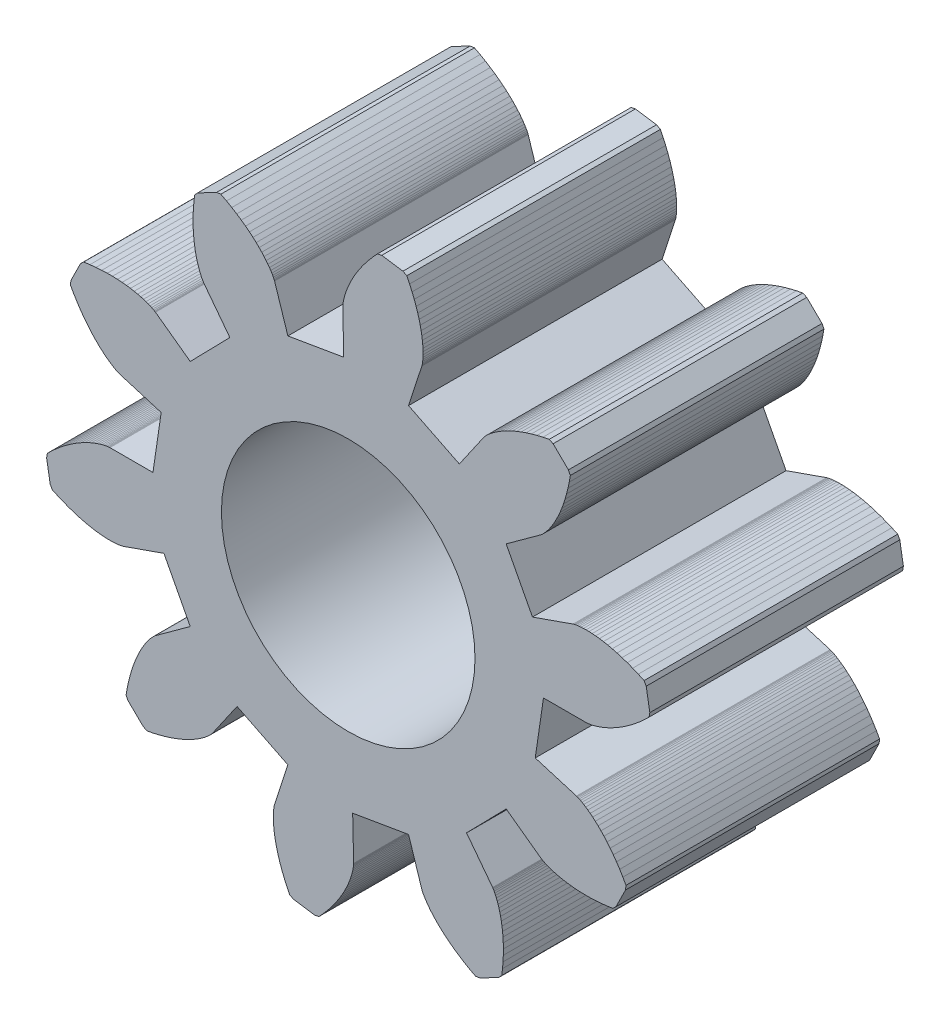
SolidWorks part; units mm, degrees
ref_plane "前基準面" through (0, 0, 0) normal (0, 0, 1) x (1, 0, 0)
ref_plane "上基準面" through (0, 0, 0) normal (0, 1, 0) x (1, 0, 0)
ref_plane "右基準面" through (0, 0, 0) normal (1, 0, 0) x (0, 0, -1)
sketch "Model" plane through (0, 0, 0) normal (0, 0, 1) x (1, 0, 0)
  line L0 (3.85, 0) -> (4.6992, 0)
  line L1 (4.6992, 0) -> (4.7049, 0.0002)
  line L2 (4.7049, 0.0002) -> (4.7163, 0.001)
  line L3 (4.7163, 0.001) -> (4.7334, 0.0029)
  line L4 (4.7334, 0.0029) -> (4.7561, 0.0061)
  line L5 (4.7561, 0.0061) -> (4.7843, 0.011)
  line L6 (4.7843, 0.011) -> (4.8179, 0.0182)
  line L7 (4.8179, 0.0182) -> (4.8567, 0.0279)
  line L8 (4.8567, 0.0279) -> (4.9007, 0.0405)
  line L9 (4.9007, 0.0405) -> (4.9497, 0.0565)
  line L10 (4.9497, 0.0565) -> (5.0035, 0.0761)
  line L11 (5.0035, 0.0761) -> (5.0619, 0.0997)
  line L12 (5.0619, 0.0997) -> (5.1247, 0.1276)
  line L13 (5.1247, 0.1276) -> (5.1915, 0.1603)
  line L14 (5.1915, 0.1603) -> (5.2623, 0.1979)
  line L15 (5.2623, 0.1979) -> (5.3367, 0.2409)
  line L16 (5.3367, 0.2409) -> (5.4143, 0.2894)
  line L17 (5.4143, 0.2894) -> (5.495, 0.3439)
  line L18 (5.495, 0.3439) -> (5.5783, 0.4044)
  line L19 (5.5783, 0.4044) -> (5.664, 0.4714)
  line L20 (5.664, 0.4714) -> (5.7517, 0.545)
  line L21 (5.7517, 0.545) -> (5.8411, 0.6255)
  line L22 (5.8411, 0.6255) -> (5.9317, 0.713)
  line L23 (5.9317, 0.713) -> (5.9468, 0.7975)
  line L24 (5.9468, 0.7975) -> (5.876, 1.2136)
  line L25 (5.876, 1.2136) -> (5.8338, 1.2884)
  line L26 (5.8338, 1.2884) -> (5.7194, 1.341)
  line L27 (5.7194, 1.341) -> (5.6085, 1.3874)
  line L28 (5.6085, 1.3874) -> (5.5014, 1.4279)
  line L29 (5.5014, 1.4279) -> (5.3983, 1.4627)
  line L30 (5.3983, 1.4627) -> (5.2996, 1.4924)
  line L31 (5.2996, 1.4924) -> (5.2055, 1.517)
  line L32 (5.2055, 1.517) -> (5.1161, 1.5372)
  line L33 (5.1161, 1.5372) -> (5.0318, 1.5531)
  line L34 (5.0318, 1.5531) -> (4.9525, 1.5653)
  line L35 (4.9525, 1.5653) -> (4.8786, 1.574)
  line L36 (4.8786, 1.574) -> (4.8102, 1.5796)
  line L37 (4.8102, 1.5796) -> (4.7473, 1.5826)
  line L38 (4.7473, 1.5826) -> (4.69, 1.5833)
  line L39 (4.69, 1.5833) -> (4.6385, 1.5821)
  line L40 (4.6385, 1.5821) -> (4.5928, 1.5795)
  line L41 (4.5928, 1.5795) -> (4.5529, 1.5758)
  line L42 (4.5529, 1.5758) -> (4.5188, 1.5714)
  line L43 (4.5188, 1.5714) -> (4.4906, 1.5668)
  line L44 (4.4906, 1.5668) -> (4.4681, 1.5624)
  line L45 (4.4681, 1.5624) -> (4.4514, 1.5584)
  line L46 (4.4514, 1.5584) -> (4.4404, 1.5554)
  line L47 (4.4404, 1.5554) -> (4.4349, 1.5537)
  line L48 (4.4349, 1.5537) -> (3.6335, 1.273)
  line L49 (3.6335, 1.273) -> (3.1147, 2.263)
  line L50 (3.1147, 2.263) -> (3.8017, 2.7621)
  line L51 (3.8017, 2.7621) -> (3.8062, 2.7657)
  line L52 (3.8062, 2.7657) -> (3.815, 2.773)
  line L53 (3.815, 2.773) -> (3.8277, 2.7845)
  line L54 (3.8277, 2.7845) -> (3.8442, 2.8004)
  line L55 (3.8442, 2.8004) -> (3.8641, 2.821)
  line L56 (3.8641, 2.821) -> (3.887, 2.8466)
  line L57 (3.887, 2.8466) -> (3.9128, 2.8773)
  line L58 (3.9128, 2.8773) -> (3.941, 2.9134)
  line L59 (3.941, 2.9134) -> (3.9712, 2.9551)
  line L60 (3.9712, 2.9551) -> (4.0032, 3.0026)
  line L61 (4.0032, 3.0026) -> (4.0366, 3.056)
  line L62 (4.0366, 3.056) -> (4.0709, 3.1155)
  line L63 (4.0709, 3.1155) -> (4.1058, 3.1812)
  line L64 (4.1058, 3.1812) -> (4.141, 3.2532)
  line L65 (4.141, 3.2532) -> (4.1759, 3.3317)
  line L66 (4.1759, 3.3317) -> (4.2102, 3.4166)
  line L67 (4.2102, 3.4166) -> (4.2434, 3.5081)
  line L68 (4.2434, 3.5081) -> (4.2753, 3.6061)
  line L69 (4.2753, 3.6061) -> (4.3052, 3.7106)
  line L70 (4.3052, 3.7106) -> (4.3329, 3.8217)
  line L71 (4.3329, 3.8217) -> (4.3579, 3.9393)
  line L72 (4.3579, 3.9393) -> (4.3797, 4.0633)
  line L73 (4.3797, 4.0633) -> (4.3423, 4.1406)
  line L74 (4.3423, 4.1406) -> (4.0404, 4.4357)
  line L75 (4.0404, 4.4357) -> (3.9623, 4.4713)
  line L76 (3.9623, 4.4713) -> (3.8388, 4.4466)
  line L77 (3.8388, 4.4466) -> (3.7218, 4.419)
  line L78 (3.7218, 4.419) -> (3.6114, 4.3888)
  line L79 (3.6114, 4.3888) -> (3.5076, 4.3564)
  line L80 (3.5076, 4.3564) -> (3.4103, 4.3224)
  line L81 (3.4103, 4.3224) -> (3.3196, 4.287)
  line L82 (3.3196, 4.287) -> (3.2355, 4.2508)
  line L83 (3.2355, 4.2508) -> (3.1579, 4.2141)
  line L84 (3.1579, 4.2141) -> (3.0867, 4.1774)
  line L85 (3.0867, 4.1774) -> (3.0218, 4.1409)
  line L86 (3.0218, 4.1409) -> (2.963, 4.1053)
  line L87 (2.963, 4.1053) -> (2.9104, 4.0707)
  line L88 (2.9104, 4.0707) -> (2.8637, 4.0376)
  line L89 (2.8637, 4.0376) -> (2.8227, 4.0064)
  line L90 (2.8227, 4.0064) -> (2.7873, 3.9774)
  line L91 (2.7873, 3.9774) -> (2.7571, 3.951)
  line L92 (2.7571, 3.951) -> (2.7321, 3.9274)
  line L93 (2.7321, 3.9274) -> (2.712, 3.9071)
  line L94 (2.712, 3.9071) -> (2.6965, 3.8903)
  line L95 (2.6965, 3.8903) -> (2.6852, 3.8773)
  line L96 (2.6852, 3.8773) -> (2.6781, 3.8683)
  line L97 (2.6781, 3.8683) -> (2.6746, 3.8638)
  line L98 (2.6746, 3.8638) -> (2.1913, 3.1655)
  line L99 (2.1913, 3.1655) -> (1.1897, 3.6616)
  line L100 (1.1897, 3.6616) -> (1.4521, 4.4692)
  line L101 (1.4521, 4.4692) -> (1.4537, 4.4747)
  line L102 (1.4537, 4.4747) -> (1.4564, 4.4858)
  line L103 (1.4564, 4.4858) -> (1.46, 4.5026)
  line L104 (1.46, 4.5026) -> (1.4639, 4.5252)
  line L105 (1.4639, 4.5252) -> (1.4679, 4.5535)
  line L106 (1.4679, 4.5535) -> (1.4715, 4.5877)
  line L107 (1.4715, 4.5877) -> (1.4743, 4.6276)
  line L108 (1.4743, 4.6276) -> (1.4758, 4.6734)
  line L109 (1.4758, 4.6734) -> (1.4758, 4.7249)
  line L110 (1.4758, 4.7249) -> (1.4738, 4.7822)
  line L111 (1.4738, 4.7822) -> (1.4694, 4.845)
  line L112 (1.4694, 4.845) -> (1.4622, 4.9133)
  line L113 (1.4622, 4.9133) -> (1.4518, 4.987)
  line L114 (1.4518, 4.987) -> (1.4379, 5.0659)
  line L115 (1.4379, 5.0659) -> (1.42, 5.1499)
  line L116 (1.42, 5.1499) -> (1.3979, 5.2388)
  line L117 (1.3979, 5.2388) -> (1.371, 5.3323)
  line L118 (1.371, 5.3323) -> (1.3392, 5.4303)
  line L119 (1.3392, 5.4303) -> (1.3019, 5.5325)
  line L120 (1.3019, 5.5325) -> (1.259, 5.6387)
  line L121 (1.259, 5.6387) -> (1.2101, 5.7485)
  line L122 (1.2101, 5.7485) -> (1.1549, 5.8617)
  line L123 (1.1549, 5.8617) -> (1.0792, 5.9021)
  line L124 (1.0792, 5.9021) -> (0.6615, 5.9634)
  line L125 (0.6615, 5.9634) -> (0.5774, 5.9464)
  line L126 (0.5774, 5.9464) -> (0.492, 5.8538)
  line L127 (0.492, 5.8538) -> (0.4136, 5.7627)
  line L128 (0.4136, 5.7627) -> (0.342, 5.6733)
  line L129 (0.342, 5.6733) -> (0.277, 5.5861)
  line L130 (0.277, 5.5861) -> (0.2184, 5.5014)
  line L131 (0.2184, 5.5014) -> (0.1658, 5.4195)
  line L132 (0.1658, 5.4195) -> (0.119, 5.3408)
  line L133 (0.119, 5.3408) -> (0.0778, 5.2654)
  line L134 (0.0778, 5.2654) -> (0.0418, 5.1938)
  line L135 (0.0418, 5.1938) -> (0.0107, 5.1262)
  line L136 (0.0107, 5.1262) -> (-0.0159, 5.0629)
  line L137 (-0.0159, 5.0629) -> (-0.0381, 5.004)
  line L138 (-0.0381, 5.004) -> (-0.0565, 4.9497)
  line L139 (-0.0565, 4.9497) -> (-0.0713, 4.9004)
  line L140 (-0.0713, 4.9004) -> (-0.0829, 4.8561)
  line L141 (-0.0829, 4.8561) -> (-0.0918, 4.817)
  line L142 (-0.0918, 4.817) -> (-0.0981, 4.7833)
  line L143 (-0.0981, 4.7833) -> (-0.1025, 4.755)
  line L144 (-0.1025, 4.755) -> (-0.1052, 4.7322)
  line L145 (-0.1052, 4.7322) -> (-0.1066, 4.7151)
  line L146 (-0.1066, 4.7151) -> (-0.1071, 4.7037)
  line L147 (-0.1071, 4.7037) -> (-0.1072, 4.698)
  line L148 (-0.1072, 4.698) -> (-0.0879, 3.849)
  line L149 (-0.0879, 3.849) -> (-1.1897, 3.6616)
  line L150 (-1.1897, 3.6616) -> (-1.4521, 4.4692)
  line L151 (-1.4521, 4.4692) -> (-1.4541, 4.4746)
  line L152 (-1.4541, 4.4746) -> (-1.4584, 4.4852)
  line L153 (-1.4584, 4.4852) -> (-1.4654, 4.5008)
  line L154 (-1.4654, 4.5008) -> (-1.4755, 4.5214)
  line L155 (-1.4755, 4.5214) -> (-1.4889, 4.5467)
  line L156 (-1.4889, 4.5467) -> (-1.5061, 4.5764)
  line L157 (-1.5061, 4.5764) -> (-1.5274, 4.6104)
  line L158 (-1.5274, 4.6104) -> (-1.553, 4.6484)
  line L159 (-1.553, 4.6484) -> (-1.5833, 4.69)
  line L160 (-1.5833, 4.69) -> (-1.6185, 4.7351)
  line L161 (-1.6185, 4.7351) -> (-1.659, 4.7834)
  line L162 (-1.659, 4.7834) -> (-1.705, 4.8344)
  line L163 (-1.705, 4.8344) -> (-1.7567, 4.8879)
  line L164 (-1.7567, 4.8879) -> (-1.8144, 4.9436)
  line L165 (-1.8144, 4.9436) -> (-1.8782, 5.001)
  line L166 (-1.8782, 5.001) -> (-1.9484, 5.0599)
  line L167 (-1.9484, 5.0599) -> (-2.0251, 5.1198)
  line L168 (-2.0251, 5.1198) -> (-2.1084, 5.1803)
  line L169 (-2.1084, 5.1803) -> (-2.1986, 5.2412)
  line L170 (-2.1986, 5.2412) -> (-2.2957, 5.3018)
  line L171 (-2.2957, 5.3018) -> (-2.3999, 5.3619)
  line L172 (-2.3999, 5.3619) -> (-2.5111, 5.421)
  line L173 (-2.5111, 5.421) -> (-2.5961, 5.4093)
  line L174 (-2.5961, 5.4093) -> (-2.97, 5.2134)
  line L175 (-2.97, 5.2134) -> (-3.0281, 5.1501)
  line L176 (-3.0281, 5.1501) -> (-3.0427, 5.025)
  line L177 (-3.0427, 5.025) -> (-3.0526, 4.9052)
  line L178 (-3.0526, 4.9052) -> (-3.058, 4.7909)
  line L179 (-3.058, 4.7909) -> (-3.0593, 4.6821)
  line L180 (-3.0593, 4.6821) -> (-3.057, 4.5791)
  line L181 (-3.057, 4.5791) -> (-3.0514, 4.4819)
  line L182 (-3.0514, 4.4819) -> (-3.0429, 4.3907)
  line L183 (-3.0429, 4.3907) -> (-3.032, 4.3056)
  line L184 (-3.032, 4.3056) -> (-3.0191, 4.2265)
  line L185 (-3.0191, 4.2265) -> (-3.0045, 4.1535)
  line L186 (-3.0045, 4.1535) -> (-2.9887, 4.0866)
  line L187 (-2.9887, 4.0866) -> (-2.9721, 4.0259)
  line L188 (-2.9721, 4.0259) -> (-2.9551, 3.9712)
  line L189 (-2.9551, 3.9712) -> (-2.9381, 3.9226)
  line L190 (-2.9381, 3.9226) -> (-2.9214, 3.8799)
  line L191 (-2.9214, 3.8799) -> (-2.9056, 3.8431)
  line L192 (-2.9056, 3.8431) -> (-2.8909, 3.8121)
  line L193 (-2.8909, 3.8121) -> (-2.8778, 3.7866)
  line L194 (-2.8778, 3.7866) -> (-2.8666, 3.7666)
  line L195 (-2.8666, 3.7666) -> (-2.8577, 3.752)
  line L196 (-2.8577, 3.752) -> (-2.8514, 3.7424)
  line L197 (-2.8514, 3.7424) -> (-2.8481, 3.7377)
  line L198 (-2.8481, 3.7377) -> (-2.3335, 3.0623)
  line L199 (-2.3335, 3.0623) -> (-3.1147, 2.263)
  line L200 (-3.1147, 2.263) -> (-3.8017, 2.7621)
  line L201 (-3.8017, 2.7621) -> (-3.8065, 2.7653)
  line L202 (-3.8065, 2.7653) -> (-3.8162, 2.7713)
  line L203 (-3.8162, 2.7713) -> (-3.8311, 2.7799)
  line L204 (-3.8311, 2.7799) -> (-3.8513, 2.7906)
  line L205 (-3.8513, 2.7906) -> (-3.877, 2.8032)
  line L206 (-3.877, 2.8032) -> (-3.9084, 2.8171)
  line L207 (-3.9084, 2.8171) -> (-3.9456, 2.8321)
  line L208 (-3.9456, 2.8321) -> (-3.9886, 2.8478)
  line L209 (-3.9886, 2.8478) -> (-4.0376, 2.8637)
  line L210 (-4.0376, 2.8637) -> (-4.0927, 2.8795)
  line L211 (-4.0927, 2.8795) -> (-4.1538, 2.8947)
  line L212 (-4.1538, 2.8947) -> (-4.221, 2.9089)
  line L213 (-4.221, 2.9089) -> (-4.2943, 2.9218)
  line L214 (-4.2943, 2.9218) -> (-4.3736, 2.933)
  line L215 (-4.3736, 2.933) -> (-4.459, 2.9419)
  line L216 (-4.459, 2.9419) -> (-4.5504, 2.9483)
  line L217 (-4.5504, 2.9483) -> (-4.6477, 2.9517)
  line L218 (-4.6477, 2.9517) -> (-4.7507, 2.9517)
  line L219 (-4.7507, 2.9517) -> (-4.8594, 2.9479)
  line L220 (-4.8594, 2.9479) -> (-4.9736, 2.9399)
  line L221 (-4.9736, 2.9399) -> (-5.0932, 2.9273)
  line L222 (-5.0932, 2.9273) -> (-5.2179, 2.9097)
  line L223 (-5.2179, 2.9097) -> (-5.2798, 2.8503)
  line L224 (-5.2798, 2.8503) -> (-5.4671, 2.472)
  line L225 (-5.4671, 2.472) -> (-5.4769, 2.3867)
  line L226 (-5.4769, 2.3867) -> (-5.4153, 2.2769)
  line L227 (-5.4153, 2.2769) -> (-5.3528, 2.1741)
  line L228 (-5.3528, 2.1741) -> (-5.29, 2.0784)
  line L229 (-5.29, 2.0784) -> (-5.2271, 1.9897)
  line L230 (-5.2271, 1.9897) -> (-5.1647, 1.9077)
  line L231 (-5.1647, 1.9077) -> (-5.103, 1.8324)
  line L232 (-5.103, 1.8324) -> (-5.0426, 1.7636)
  line L233 (-5.0426, 1.7636) -> (-4.9837, 1.7011)
  line L234 (-4.9837, 1.7011) -> (-4.9267, 1.6447)
  line L235 (-4.9267, 1.6447) -> (-4.872, 1.5942)
  line L236 (-4.872, 1.5942) -> (-4.82, 1.5494)
  line L237 (-4.82, 1.5494) -> (-4.7708, 1.5101)
  line L238 (-4.7708, 1.5101) -> (-4.7249, 1.4758)
  line L239 (-4.7249, 1.4758) -> (-4.6826, 1.4465)
  line L240 (-4.6826, 1.4465) -> (-4.6441, 1.4217)
  line L241 (-4.6441, 1.4217) -> (-4.6096, 1.4013)
  line L242 (-4.6096, 1.4013) -> (-4.5795, 1.3848)
  line L243 (-4.5795, 1.3848) -> (-4.5539, 1.3719)
  line L244 (-4.5539, 1.3719) -> (-4.5331, 1.3623)
  line L245 (-4.5331, 1.3623) -> (-4.5173, 1.3557)
  line L246 (-4.5173, 1.3557) -> (-4.5066, 1.3516)
  line L247 (-4.5066, 1.3516) -> (-4.5012, 1.3498)
  line L248 (-4.5012, 1.3498) -> (-3.6878, 1.1058)
  line L249 (-3.6878, 1.1058) -> (-3.85, 0)
  line L250 (-3.85, 0) -> (-4.6992, 0)
  line L251 (-4.6992, 0) -> (-4.7049, -0.0002)
  line L252 (-4.7049, -0.0002) -> (-4.7163, -0.001)
  line L253 (-4.7163, -0.001) -> (-4.7334, -0.0029)
  line L254 (-4.7334, -0.0029) -> (-4.7561, -0.0061)
  line L255 (-4.7561, -0.0061) -> (-4.7843, -0.011)
  line L256 (-4.7843, -0.011) -> (-4.8179, -0.0182)
  line L257 (-4.8179, -0.0182) -> (-4.8567, -0.0279)
  line L258 (-4.8567, -0.0279) -> (-4.9007, -0.0405)
  line L259 (-4.9007, -0.0405) -> (-4.9497, -0.0565)
  line L260 (-4.9497, -0.0565) -> (-5.0035, -0.0761)
  line L261 (-5.0035, -0.0761) -> (-5.0619, -0.0997)
  line L262 (-5.0619, -0.0997) -> (-5.1247, -0.1276)
  line L263 (-5.1247, -0.1276) -> (-5.1915, -0.1603)
  line L264 (-5.1915, -0.1603) -> (-5.2623, -0.1979)
  line L265 (-5.2623, -0.1979) -> (-5.3367, -0.2409)
  line L266 (-5.3367, -0.2409) -> (-5.4143, -0.2894)
  line L267 (-5.4143, -0.2894) -> (-5.495, -0.3439)
  line L268 (-5.495, -0.3439) -> (-5.5783, -0.4044)
  line L269 (-5.5783, -0.4044) -> (-5.664, -0.4714)
  line L270 (-5.664, -0.4714) -> (-5.7517, -0.545)
  line L271 (-5.7517, -0.545) -> (-5.8411, -0.6255)
  line L272 (-5.8411, -0.6255) -> (-5.9317, -0.713)
  line L273 (-5.9317, -0.713) -> (-5.9468, -0.7975)
  line L274 (-5.9468, -0.7975) -> (-5.876, -1.2136)
  line L275 (-5.876, -1.2136) -> (-5.8338, -1.2884)
  line L276 (-5.8338, -1.2884) -> (-5.7194, -1.341)
  line L277 (-5.7194, -1.341) -> (-5.6085, -1.3874)
  line L278 (-5.6085, -1.3874) -> (-5.5014, -1.4279)
  line L279 (-5.5014, -1.4279) -> (-5.3983, -1.4627)
  line L280 (-5.3983, -1.4627) -> (-5.2996, -1.4924)
  line L281 (-5.2996, -1.4924) -> (-5.2055, -1.517)
  line L282 (-5.2055, -1.517) -> (-5.1161, -1.5372)
  line L283 (-5.1161, -1.5372) -> (-5.0318, -1.5531)
  line L284 (-5.0318, -1.5531) -> (-4.9525, -1.5653)
  line L285 (-4.9525, -1.5653) -> (-4.8786, -1.574)
  line L286 (-4.8786, -1.574) -> (-4.8102, -1.5796)
  line L287 (-4.8102, -1.5796) -> (-4.7473, -1.5826)
  line L288 (-4.7473, -1.5826) -> (-4.69, -1.5833)
  line L289 (-4.69, -1.5833) -> (-4.6385, -1.5821)
  line L290 (-4.6385, -1.5821) -> (-4.5928, -1.5795)
  line L291 (-4.5928, -1.5795) -> (-4.5529, -1.5758)
  line L292 (-4.5529, -1.5758) -> (-4.5188, -1.5714)
  line L293 (-4.5188, -1.5714) -> (-4.4906, -1.5668)
  line L294 (-4.4906, -1.5668) -> (-4.4681, -1.5624)
  line L295 (-4.4681, -1.5624) -> (-4.4514, -1.5584)
  line L296 (-4.4514, -1.5584) -> (-4.4404, -1.5554)
  line L297 (-4.4404, -1.5554) -> (-4.4349, -1.5537)
  line L298 (-4.4349, -1.5537) -> (-3.6335, -1.273)
  line L299 (-3.6335, -1.273) -> (-3.1147, -2.263)
  line L300 (-3.1147, -2.263) -> (-3.8017, -2.7621)
  line L301 (-3.8017, -2.7621) -> (-3.8062, -2.7657)
  line L302 (-3.8062, -2.7657) -> (-3.815, -2.773)
  line L303 (-3.815, -2.773) -> (-3.8277, -2.7845)
  line L304 (-3.8277, -2.7845) -> (-3.8442, -2.8004)
  line L305 (-3.8442, -2.8004) -> (-3.8641, -2.821)
  line L306 (-3.8641, -2.821) -> (-3.887, -2.8466)
  line L307 (-3.887, -2.8466) -> (-3.9128, -2.8773)
  line L308 (-3.9128, -2.8773) -> (-3.941, -2.9134)
  line L309 (-3.941, -2.9134) -> (-3.9712, -2.9551)
  line L310 (-3.9712, -2.9551) -> (-4.0032, -3.0026)
  line L311 (-4.0032, -3.0026) -> (-4.0366, -3.056)
  line L312 (-4.0366, -3.056) -> (-4.0709, -3.1155)
  line L313 (-4.0709, -3.1155) -> (-4.1058, -3.1812)
  line L314 (-4.1058, -3.1812) -> (-4.141, -3.2532)
  line L315 (-4.141, -3.2532) -> (-4.1759, -3.3317)
  line L316 (-4.1759, -3.3317) -> (-4.2102, -3.4166)
  line L317 (-4.2102, -3.4166) -> (-4.2434, -3.5081)
  line L318 (-4.2434, -3.5081) -> (-4.2753, -3.6061)
  line L319 (-4.2753, -3.6061) -> (-4.3052, -3.7106)
  line L320 (-4.3052, -3.7106) -> (-4.3329, -3.8217)
  line L321 (-4.3329, -3.8217) -> (-4.3579, -3.9393)
  line L322 (-4.3579, -3.9393) -> (-4.3797, -4.0633)
  line L323 (-4.3797, -4.0633) -> (-4.3423, -4.1406)
  line L324 (-4.3423, -4.1406) -> (-4.0404, -4.4357)
  line L325 (-4.0404, -4.4357) -> (-3.9623, -4.4713)
  line L326 (-3.9623, -4.4713) -> (-3.8388, -4.4466)
  line L327 (-3.8388, -4.4466) -> (-3.7218, -4.419)
  line L328 (-3.7218, -4.419) -> (-3.6114, -4.3888)
  line L329 (-3.6114, -4.3888) -> (-3.5076, -4.3564)
  line L330 (-3.5076, -4.3564) -> (-3.4103, -4.3224)
  line L331 (-3.4103, -4.3224) -> (-3.3196, -4.287)
  line L332 (-3.3196, -4.287) -> (-3.2355, -4.2508)
  line L333 (-3.2355, -4.2508) -> (-3.1579, -4.2141)
  line L334 (-3.1579, -4.2141) -> (-3.0867, -4.1774)
  line L335 (-3.0867, -4.1774) -> (-3.0218, -4.1409)
  line L336 (-3.0218, -4.1409) -> (-2.963, -4.1053)
  line L337 (-2.963, -4.1053) -> (-2.9104, -4.0707)
  line L338 (-2.9104, -4.0707) -> (-2.8637, -4.0376)
  line L339 (-2.8637, -4.0376) -> (-2.8227, -4.0064)
  line L340 (-2.8227, -4.0064) -> (-2.7873, -3.9774)
  line L341 (-2.7873, -3.9774) -> (-2.7571, -3.951)
  line L342 (-2.7571, -3.951) -> (-2.7321, -3.9274)
  line L343 (-2.7321, -3.9274) -> (-2.712, -3.9071)
  line L344 (-2.712, -3.9071) -> (-2.6965, -3.8903)
  line L345 (-2.6965, -3.8903) -> (-2.6852, -3.8773)
  line L346 (-2.6852, -3.8773) -> (-2.6781, -3.8683)
  line L347 (-2.6781, -3.8683) -> (-2.6746, -3.8638)
  line L348 (-2.6746, -3.8638) -> (-2.1913, -3.1655)
  line L349 (-2.1913, -3.1655) -> (-1.1897, -3.6616)
  line L350 (-1.1897, -3.6616) -> (-1.4521, -4.4692)
  line L351 (-1.4521, -4.4692) -> (-1.4537, -4.4747)
  line L352 (-1.4537, -4.4747) -> (-1.4564, -4.4858)
  line L353 (-1.4564, -4.4858) -> (-1.46, -4.5026)
  line L354 (-1.46, -4.5026) -> (-1.4639, -4.5252)
  line L355 (-1.4639, -4.5252) -> (-1.4679, -4.5535)
  line L356 (-1.4679, -4.5535) -> (-1.4715, -4.5877)
  line L357 (-1.4715, -4.5877) -> (-1.4743, -4.6276)
  line L358 (-1.4743, -4.6276) -> (-1.4758, -4.6734)
  line L359 (-1.4758, -4.6734) -> (-1.4758, -4.7249)
  line L360 (-1.4758, -4.7249) -> (-1.4738, -4.7822)
  line L361 (-1.4738, -4.7822) -> (-1.4694, -4.845)
  line L362 (-1.4694, -4.845) -> (-1.4622, -4.9133)
  line L363 (-1.4622, -4.9133) -> (-1.4518, -4.987)
  line L364 (-1.4518, -4.987) -> (-1.4379, -5.0659)
  line L365 (-1.4379, -5.0659) -> (-1.42, -5.1499)
  line L366 (-1.42, -5.1499) -> (-1.3979, -5.2388)
  line L367 (-1.3979, -5.2388) -> (-1.371, -5.3323)
  line L368 (-1.371, -5.3323) -> (-1.3392, -5.4303)
  line L369 (-1.3392, -5.4303) -> (-1.3019, -5.5325)
  line L370 (-1.3019, -5.5325) -> (-1.259, -5.6387)
  line L371 (-1.259, -5.6387) -> (-1.2101, -5.7485)
  line L372 (-1.2101, -5.7485) -> (-1.1549, -5.8617)
  line L373 (-1.1549, -5.8617) -> (-1.0792, -5.9021)
  line L374 (-1.0792, -5.9021) -> (-0.6615, -5.9634)
  line L375 (-0.6615, -5.9634) -> (-0.5774, -5.9464)
  line L376 (-0.5774, -5.9464) -> (-0.492, -5.8538)
  line L377 (-0.492, -5.8538) -> (-0.4136, -5.7627)
  line L378 (-0.4136, -5.7627) -> (-0.342, -5.6733)
  line L379 (-0.342, -5.6733) -> (-0.277, -5.5861)
  line L380 (-0.277, -5.5861) -> (-0.2184, -5.5014)
  line L381 (-0.2184, -5.5014) -> (-0.1658, -5.4195)
  line L382 (-0.1658, -5.4195) -> (-0.119, -5.3408)
  line L383 (-0.119, -5.3408) -> (-0.0778, -5.2654)
  line L384 (-0.0778, -5.2654) -> (-0.0418, -5.1938)
  line L385 (-0.0418, -5.1938) -> (-0.0107, -5.1262)
  line L386 (-0.0107, -5.1262) -> (0.0159, -5.0629)
  line L387 (0.0159, -5.0629) -> (0.0381, -5.004)
  line L388 (0.0381, -5.004) -> (0.0565, -4.9497)
  line L389 (0.0565, -4.9497) -> (0.0713, -4.9004)
  line L390 (0.0713, -4.9004) -> (0.0829, -4.8561)
  line L391 (0.0829, -4.8561) -> (0.0918, -4.817)
  line L392 (0.0918, -4.817) -> (0.0981, -4.7833)
  line L393 (0.0981, -4.7833) -> (0.1025, -4.755)
  line L394 (0.1025, -4.755) -> (0.1052, -4.7322)
  line L395 (0.1052, -4.7322) -> (0.1066, -4.7151)
  line L396 (0.1066, -4.7151) -> (0.1071, -4.7037)
  line L397 (0.1071, -4.7037) -> (0.1072, -4.698)
  line L398 (0.1072, -4.698) -> (0.0879, -3.849)
  line L399 (0.0879, -3.849) -> (1.1897, -3.6616)
  line L400 (1.1897, -3.6616) -> (1.4521, -4.4692)
  line L401 (1.4521, -4.4692) -> (1.4541, -4.4746)
  line L402 (1.4541, -4.4746) -> (1.4584, -4.4852)
  line L403 (1.4584, -4.4852) -> (1.4654, -4.5008)
  line L404 (1.4654, -4.5008) -> (1.4755, -4.5214)
  line L405 (1.4755, -4.5214) -> (1.4889, -4.5467)
  line L406 (1.4889, -4.5467) -> (1.5061, -4.5764)
  line L407 (1.5061, -4.5764) -> (1.5274, -4.6104)
  line L408 (1.5274, -4.6104) -> (1.553, -4.6484)
  line L409 (1.553, -4.6484) -> (1.5833, -4.69)
  line L410 (1.5833, -4.69) -> (1.6185, -4.7351)
  line L411 (1.6185, -4.7351) -> (1.659, -4.7834)
  line L412 (1.659, -4.7834) -> (1.705, -4.8344)
  line L413 (1.705, -4.8344) -> (1.7567, -4.8879)
  line L414 (1.7567, -4.8879) -> (1.8144, -4.9436)
  line L415 (1.8144, -4.9436) -> (1.8782, -5.001)
  line L416 (1.8782, -5.001) -> (1.9484, -5.0599)
  line L417 (1.9484, -5.0599) -> (2.0251, -5.1198)
  line L418 (2.0251, -5.1198) -> (2.1084, -5.1803)
  line L419 (2.1084, -5.1803) -> (2.1986, -5.2412)
  line L420 (2.1986, -5.2412) -> (2.2957, -5.3018)
  line L421 (2.2957, -5.3018) -> (2.3999, -5.3619)
  line L422 (2.3999, -5.3619) -> (2.5111, -5.421)
  line L423 (2.5111, -5.421) -> (2.5961, -5.4093)
  line L424 (2.5961, -5.4093) -> (2.97, -5.2134)
  line L425 (2.97, -5.2134) -> (3.0281, -5.1501)
  line L426 (3.0281, -5.1501) -> (3.0427, -5.025)
  line L427 (3.0427, -5.025) -> (3.0526, -4.9052)
  line L428 (3.0526, -4.9052) -> (3.058, -4.7909)
  line L429 (3.058, -4.7909) -> (3.0593, -4.6821)
  line L430 (3.0593, -4.6821) -> (3.057, -4.5791)
  line L431 (3.057, -4.5791) -> (3.0514, -4.4819)
  line L432 (3.0514, -4.4819) -> (3.0429, -4.3907)
  line L433 (3.0429, -4.3907) -> (3.032, -4.3056)
  line L434 (3.032, -4.3056) -> (3.0191, -4.2265)
  line L435 (3.0191, -4.2265) -> (3.0045, -4.1535)
  line L436 (3.0045, -4.1535) -> (2.9887, -4.0866)
  line L437 (2.9887, -4.0866) -> (2.9721, -4.0259)
  line L438 (2.9721, -4.0259) -> (2.9551, -3.9712)
  line L439 (2.9551, -3.9712) -> (2.9381, -3.9226)
  line L440 (2.9381, -3.9226) -> (2.9214, -3.8799)
  line L441 (2.9214, -3.8799) -> (2.9056, -3.8431)
  line L442 (2.9056, -3.8431) -> (2.8909, -3.8121)
  line L443 (2.8909, -3.8121) -> (2.8778, -3.7866)
  line L444 (2.8778, -3.7866) -> (2.8666, -3.7666)
  line L445 (2.8666, -3.7666) -> (2.8577, -3.752)
  line L446 (2.8577, -3.752) -> (2.8514, -3.7424)
  line L447 (2.8514, -3.7424) -> (2.8481, -3.7377)
  line L448 (2.8481, -3.7377) -> (2.3335, -3.0623)
  line L449 (2.3335, -3.0623) -> (3.1147, -2.263)
  line L450 (3.1147, -2.263) -> (3.8017, -2.7621)
  line L451 (3.8017, -2.7621) -> (3.8065, -2.7653)
  line L452 (3.8065, -2.7653) -> (3.8162, -2.7713)
  line L453 (3.8162, -2.7713) -> (3.8311, -2.7799)
  line L454 (3.8311, -2.7799) -> (3.8513, -2.7906)
  line L455 (3.8513, -2.7906) -> (3.877, -2.8032)
  line L456 (3.877, -2.8032) -> (3.9084, -2.8171)
  line L457 (3.9084, -2.8171) -> (3.9456, -2.8321)
  line L458 (3.9456, -2.8321) -> (3.9886, -2.8478)
  line L459 (3.9886, -2.8478) -> (4.0376, -2.8637)
  line L460 (4.0376, -2.8637) -> (4.0927, -2.8795)
  line L461 (4.0927, -2.8795) -> (4.1538, -2.8947)
  line L462 (4.1538, -2.8947) -> (4.221, -2.9089)
  line L463 (4.221, -2.9089) -> (4.2943, -2.9218)
  line L464 (4.2943, -2.9218) -> (4.3736, -2.933)
  line L465 (4.3736, -2.933) -> (4.459, -2.9419)
  line L466 (4.459, -2.9419) -> (4.5504, -2.9483)
  line L467 (4.5504, -2.9483) -> (4.6477, -2.9517)
  line L468 (4.6477, -2.9517) -> (4.7507, -2.9517)
  line L469 (4.7507, -2.9517) -> (4.8594, -2.9479)
  line L470 (4.8594, -2.9479) -> (4.9736, -2.9399)
  line L471 (4.9736, -2.9399) -> (5.0932, -2.9273)
  line L472 (5.0932, -2.9273) -> (5.2179, -2.9097)
  line L473 (5.2179, -2.9097) -> (5.2798, -2.8503)
  line L474 (5.2798, -2.8503) -> (5.4671, -2.472)
  line L475 (5.4671, -2.472) -> (5.4769, -2.3867)
  line L476 (5.4769, -2.3867) -> (5.4153, -2.2769)
  line L477 (5.4153, -2.2769) -> (5.3528, -2.1741)
  line L478 (5.3528, -2.1741) -> (5.29, -2.0784)
  line L479 (5.29, -2.0784) -> (5.2271, -1.9897)
  line L480 (5.2271, -1.9897) -> (5.1647, -1.9077)
  line L481 (5.1647, -1.9077) -> (5.103, -1.8324)
  line L482 (5.103, -1.8324) -> (5.0426, -1.7636)
  line L483 (5.0426, -1.7636) -> (4.9837, -1.7011)
  line L484 (4.9837, -1.7011) -> (4.9267, -1.6447)
  line L485 (4.9267, -1.6447) -> (4.872, -1.5942)
  line L486 (4.872, -1.5942) -> (4.82, -1.5494)
  line L487 (4.82, -1.5494) -> (4.7708, -1.5101)
  line L488 (4.7708, -1.5101) -> (4.7249, -1.4758)
  line L489 (4.7249, -1.4758) -> (4.6826, -1.4465)
  line L490 (4.6826, -1.4465) -> (4.6441, -1.4217)
  line L491 (4.6441, -1.4217) -> (4.6096, -1.4013)
  line L492 (4.6096, -1.4013) -> (4.5795, -1.3848)
  line L493 (4.5795, -1.3848) -> (4.5539, -1.3719)
  line L494 (4.5539, -1.3719) -> (4.5331, -1.3623)
  line L495 (4.5331, -1.3623) -> (4.5173, -1.3557)
  line L496 (4.5173, -1.3557) -> (4.5066, -1.3516)
  line L497 (4.5066, -1.3516) -> (4.5012, -1.3498)
  line L498 (4.5012, -1.3498) -> (3.6878, -1.1058)
  line L499 (3.6878, -1.1058) -> (3.85, 0)
  line L696 (10, 0) -> (-10, 0) construction
  line L697 (0, 10) -> (0, -10) construction
  circle A0 centre (4.9292, 0.8385) radius 0.3925 construction
  circle A1 centre (0, 0) radius 5 construction
  circle A2 centre (0, 0) radius 6 construction
  circle A3 centre (0, 0) radius 4.6985 construction
  circle A4 centre (0, 0) radius 2.5
  dimension "D1" = 10
  dimension "D2" = 5
extrude "填料-伸長1" add sketch "Model" along normal blind 5
